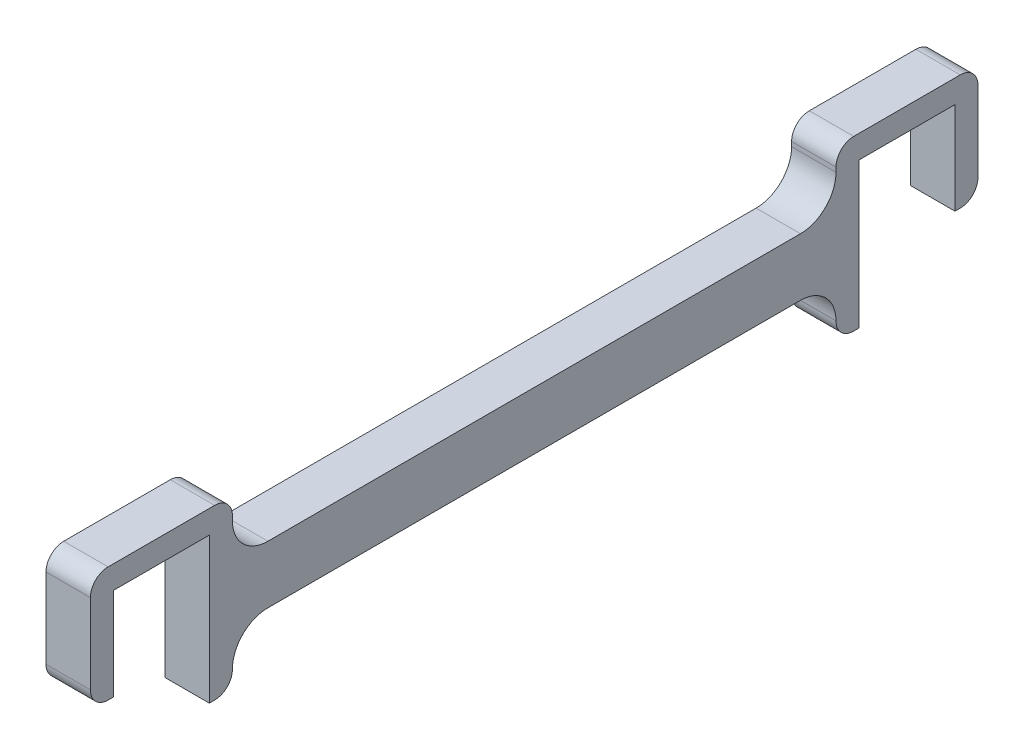
SolidWorks part; units mm, degrees
ref_plane "Ön Düzlem" through (0, 0, 0) normal (1, 0, 0) x (0, 1, 0)
ref_plane "Üst Düzlem" through (0, 0, 0) normal (0, 0, 1) x (0, 1, 0)
ref_plane "Sağ Düzlem" through (0, 0, 0) normal (0, 1, 0) x (-1, 0, 0)
sketch "Sketch1" plane through (0, 0, 0) normal (1, 0, 0) x (0, -1, 0)
  line L1 (-87, -13.4) -> (-81, -13.4)
  line L4 (-87, -20) -> (-87, -19.99)
  line L7 (-89, 0) -> (-98, 0)
  line L9 (-97.5, -16) -> (-98, -16)
  line L11 (-100, -14) -> (-100, -2)
  line L12 (-50, 0) -> (-50, -100) construction
  line L13 (-81, -13.4) -> (-81, -14.01)
  line L14 (-87, -20) -> (-87, -80)
  line L15 (-100, -50) -> (8.7692, -50) construction
  line L16 (-97.4, -13.4) -> (-87, -13.4)
  line L17 (-93.5, -20) -> (-93.5, -80)
  line L18 (-97.4, -2.6) -> (-97.4, -13.4)
  line L19 (-97.4, -2.6) -> (-87, -2.6)
  line L20 (-87, -2.6) -> (-87, -2)
  line L21 (-81, -85.99) -> (-81, -86)
  line L24 (-83.01, -16) -> (-83, -16)
  line L26 (-83, -16) -> (-82.99, -16)
  line L29 (-81, -14.01) -> (-81, -14)
  line L30 (-83, -84) -> (-82.99, -84)
  line L31 (-83.01, -84) -> (-83, -84)
  line L32 (-87, -97.4) -> (-87, -98)
  line L33 (-97.4, -97.4) -> (-87, -97.4)
  line L34 (-97.4, -97.4) -> (-97.4, -86.6)
  line L35 (-97.4, -86.6) -> (-87, -86.6)
  line L36 (-81, -86.6) -> (-81, -85.99)
  line L37 (-100, -86) -> (-100, -98)
  line L38 (-97.5, -84) -> (-98, -84)
  line L39 (-89, -100) -> (-98, -100)
  line L40 (-87, -80) -> (-87, -80.01)
  line L41 (-87, -86.6) -> (-81, -86.6)
  arc A0 (-97.5, -16) -> (-93.5, -20) centre (-97.5, -20) cw
  arc A1 (-87, -2) -> (-89, 0) centre (-89, -2) ccw
  arc A2 (-98, 0) -> (-100, -2) centre (-98, -2) ccw
  arc A3 (-98, -16) -> (-100, -14) centre (-98, -14) cw
  arc A4 (-87, -19.99) -> (-83.01, -16) centre (-83.01, -19.99) cw
  arc A5 (-82.99, -16) -> (-81, -14.01) centre (-82.99, -14.01) ccw
  arc A6 (-82.99, -84) -> (-81, -85.99) centre (-82.99, -85.99) cw
  arc A7 (-87, -80.01) -> (-83.01, -84) centre (-83.01, -80.01) ccw
  arc A8 (-98, -84) -> (-100, -86) centre (-98, -86) ccw
  arc A9 (-98, -100) -> (-100, -98) centre (-98, -98) cw
  arc A10 (-87, -98) -> (-89, -100) centre (-89, -98) cw
  arc A11 (-97.5, -84) -> (-93.5, -80) centre (-97.5, -80) ccw
  point P7 (-87, 0)
  point P11 (-100, 0)
  point P25 (-100, -16)
  point P63 (-93.5, -50)
  point P65 (-87, -50)
  point P66 (-100, -84)
  point P67 (-100, -100)
  point P68 (-87, -100)
  dimension "D1" = 4
  dimension "D2" = 2
  dimension "D3" = 3.99
  dimension "D4" = 1.99
extrude "Boss-Extrude1" add sketch "Sketch1" along normal blind 5 contours A11 L38 A8 L37 A9 L39 A10 L32 L33 L34 L35 L41 L36 L21 A6 L30 L31 A7 L40 L14 L4 A4 L24 L26 A5 L13 L1 L16 L18 L19 L20 A1 L7 A2 L11 A3 L9 A0 L17
